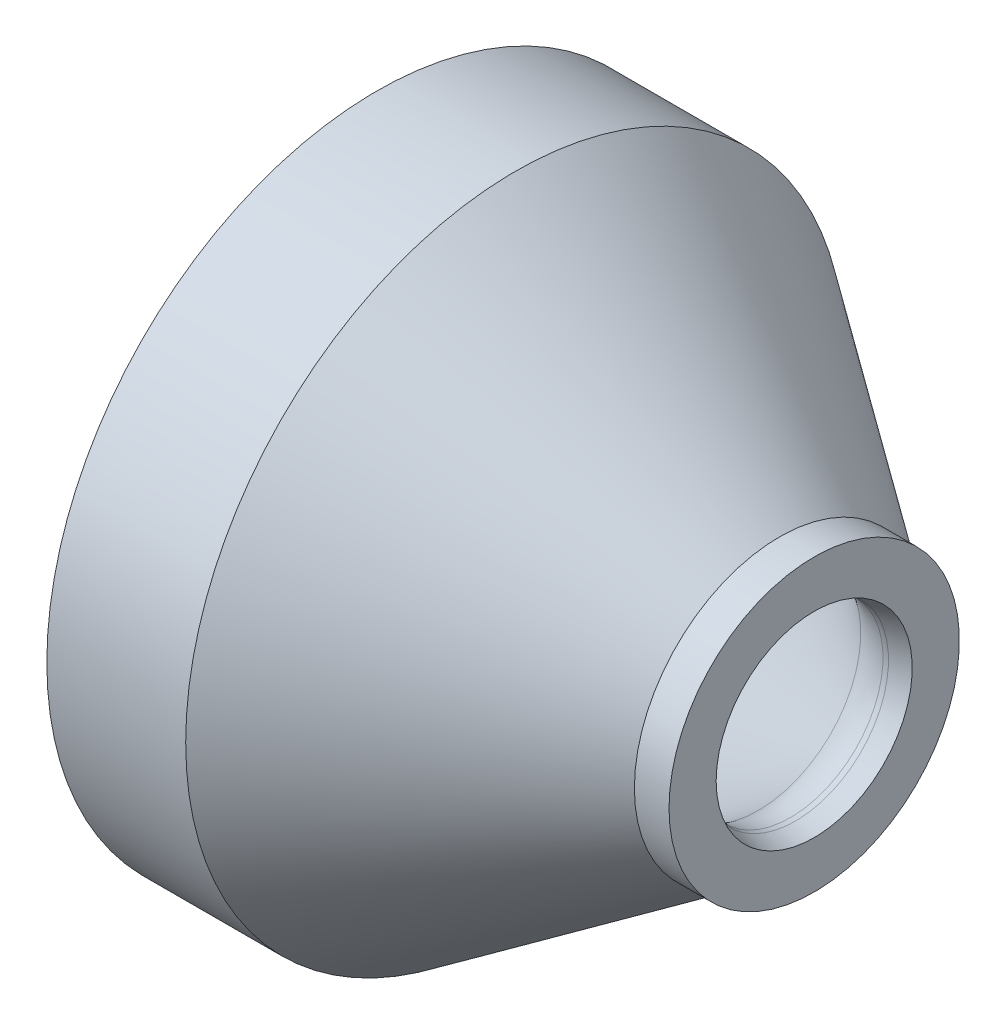
SolidWorks part; units mm, degrees
ref_plane "Front Plane" through (0, 0, 0) normal (0, 0, 1) x (1, 0, 0)
ref_plane "Top Plane" through (0, 0, 0) normal (0, 1, 0) x (1, 0, 0)
ref_plane "Right Plane" through (0, 0, 0) normal (1, 0, 0) x (0, 0, -1)
sketch "Sketch1" plane through (0, 0, 0) normal (0, 0, 1) x (1, 0, 0)
  line L0 (18.7064, 44.45) -> (0, 44.45)
  line L1 (0, 44.45) -> (0, 41.275)
  line L2 (0, 41.275) -> (12.7, 41.275)
  line L3 (12.7, 41.275) -> (12.7, 38.1)
  line L4 (19.9844, 35.8032) -> (51.3739, 13.8241)
  line L5 (56.402, 12.5325) -> (58.9228, 13.208)
  line L6 (18.7064, 44.45) -> (54.2559, 19.558)
  line L7 (54.2559, 19.558) -> (58.9228, 19.558)
  line L8 (58.9228, 13.208) -> (58.9228, 19.558)
  line L9 (0, 0) -> (17.338, 0) construction
  arc A0 (12.7, 38.1) -> (19.9844, 35.8032) centre (12.7, 25.4) cw
  arc A1 (51.3739, 13.8241) -> (55.7446, 12.446) centre (55.7446, 20.066) ccw
  arc A2 (55.7446, 12.446) -> (56.402, 12.5325) centre (55.7446, 14.986) ccw
  dimension "D1" = 12.7
  dimension "D10" = 7.62
  dimension "D11" = 2.54
  dimension "D2" = 3.175
  dimension "D3" = 41.275
  dimension "D4" = 3.175
  dimension "D5" = 12.446
  dimension "D6" = 13.208
  dimension "D7" = 15
  dimension "D8" = 35
  dimension "D9" = 12.7
  dimension "D12" = 6.35
  dimension "D13" = 6.35
revolve "Revolve1" add sketch "Sketch1" angle 360 about L9
